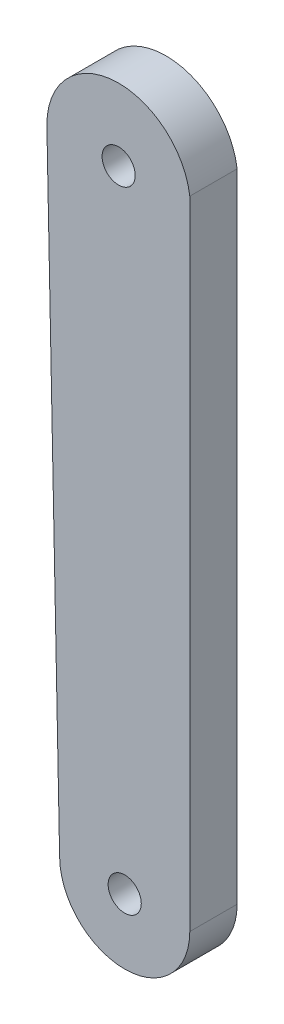
SolidWorks part; units mm, degrees
ref_plane "Front Plane" through (0, 0, 0) normal (0, 0, 1) x (1, 0, 0)
ref_plane "Top Plane" through (0, 0, 0) normal (0, 1, 0) x (1, 0, 0)
ref_plane "Right Plane" through (0, 0, 0) normal (1, 0, 0) x (0, 0, -1)
sketch "Sketch1" plane through (0, 0, 0) normal (0, 0, 1) x (1, 0, 0)
  line L6 (-0.0007, -8.0067) -> (-0.0007, 45.8123)
  line L8 (-11.0007, -8.0067) -> (-12.0773, 45.0161)
  arc A1 (-11.0007, -8.0067) -> (-0.0007, -8.0067) centre (-5.5007, -8.0067) ccw
  circle A3 centre (-5.5007, -8.0067) radius 1.4
  circle A4 centre (-6.0128, 45.0161) radius 1.4
  arc A5 (-0.0007, 44.2199) -> (-12.0723, 44.7699) centre (-6.0128, 45.0161) ccw
  point P8 (-5.0007, -13.4839)
  dimension "D4" = 11
  dimension "D3" = 2.8
  dimension "D6" = 2.8
extrude "Boss-Extrude1" add sketch "Sketch1" along normal blind 4 contours L6 A5 L8 A1 A3 A4
